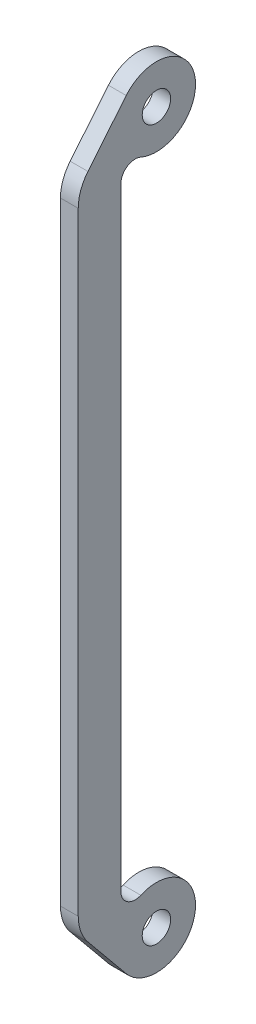
SolidWorks part; units mm, degrees
ref_plane "Front Plane" through (0, 0, 0) normal (0, 0, 1) x (1, 0, 0)
ref_plane "Top Plane" through (0, 0, 0) normal (0, 1, 0) x (1, 0, 0)
ref_plane "Right Plane" through (0, 0, 0) normal (1, 0, 0) x (0, 0, -1)
sketch "Sketch1" plane through (0, 0, 0) normal (0, 1, 0) x (1, 0, 0)
  line L3 (13.7477, -10) -> (186.2523, -10)
  line L5 (13.7477, -22) -> (186.2523, -22)
  line L6 (193.8697, -19.2722) -> (206.9827, -8.4996)
  line L8 (-6.9827, -8.4996) -> (6.1303, -19.2722)
  circle A0 centre (0, 0) radius 4
  arc A1 (10.0817, -4.4) -> (-6.9827, -8.4996) centre (0, 0) ccw
  circle A2 centre (200, 0) radius 4
  arc A3 (206.9827, -8.4996) -> (189.9183, -4.4) centre (200, 0) ccw
  arc A4 (10.0817, -4.4) -> (13.7477, -10) centre (13.7477, -6) ccw
  arc A5 (186.2523, -10) -> (189.9183, -4.4) centre (186.2523, -6) ccw
  arc A7 (186.2523, -22) -> (193.8697, -19.2722) centre (186.2523, -10) ccw
  arc A8 (6.1303, -19.2722) -> (13.7477, -22) centre (13.7477, -10) ccw
  dimension "D1" = 8
  dimension "D2" = 22
  dimension "D4" = 8
  dimension "D5" = 22
  dimension "D6" = 8
  dimension "D7" = 8
  dimension "D14" = 24
  dimension "D10" = 187.7394
  dimension "D11" = 172.5045
  dimension "D12" = 12
  dimension "D3" = 200
  dimension "D8" = 213.9653
  dimension "D9" = 172.5045
extrude "Boss-Extrude1" add sketch "Sketch1" along normal blind 5
move or copy body "Body-Move/Copy1" bodies to move or copy 101 copy no rotation origin (100, 2.5, 0) rotation axis (0, 0, 1) rotation angle 90
